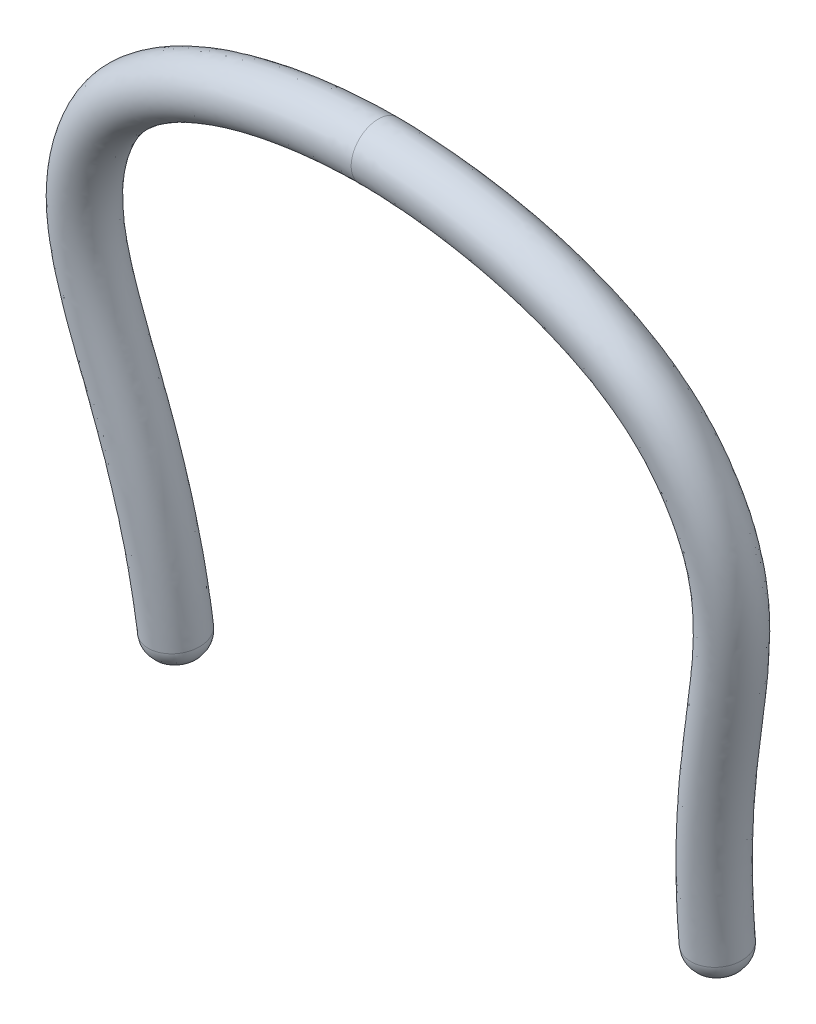
SolidWorks part; units mm, degrees
material "Oak"
ref_plane "Front Plane" through (0, 0, 0) normal (0, 0, 1) x (1, 0, 0)
ref_plane "Top Plane" through (0, 0, 0) normal (0, 1, 0) x (1, 0, 0)
ref_plane "Right Plane" through (0, 0, 0) normal (1, 0, 0) x (0, 0, -1)
sketch "Sketch2" plane through (0, 0, 0) normal (0, 0, 1) x (1, 0, 0)
  line L0 (0, 200.6909) -> (0, -79.3091) construction
  line L1 (0, -79.3091) -> (125, -79.3091) construction
  line L2 (125, -166.4594) -> (125, 8.4065) construction
  line L3 (68.3083, 200.6909) -> (-68.3083, 200.6909) construction
  line L4 (261.2069, -77.906) -> (-4.2693, 381.9124) construction
  spline S0 degree 3 poles (0, 200.6909) (45, 200.6909) (115.0329, 181.7841) (168.8493, 74.8741) (125, 25.6909) (125, -79.3091) knots 0 0 0 0 0.361342 0.461342 1 1 1 1
  point P3 (135, 140.6909)
  dimension "D5" = 60
  dimension "D6" = 350
  dimension "D7" = 350
  dimension "D8" = 150
  dimension "D1" = 125
  dimension "D2" = 280
  dimension "D3" = 135
  dimension "D4" = 60
sketch "Sketch5" plane through (0, 0, 0) normal (1, 0, 0) x (0, 0, -1)
  line L0 (0, 200.6909) -> (0, -79.3091) construction
  line L1 (0, 200.6909) -> (0, -79.3091) construction
  line L2 (0, 200.6909) -> (-32.5358, 200.6909) construction
  arc A0 (0, -79.3091) -> (-32.5358, 200.6909) centre (-11736.5663, -1301.1976) ccw
curve "Curve2"
sketch "Sketch7" plane through (0, 0, 0) normal (1, 0, 0) x (0, 0, -1)
  circle A0 centre (-32.5358, 200.6909) radius 12.5
sweep "Sweep1" add profiles "Sketch7" path "Curve2"
mirror "Mirror1" about plane through (0, 200.6909, 32.5358) normal (1, 0, 0) of "Sweep1"
fillet "Fillet1" radius 10 2 edges at (-123.4482, -78.0248, -12.3366) (123.4482, -78.0248, -12.3366)
